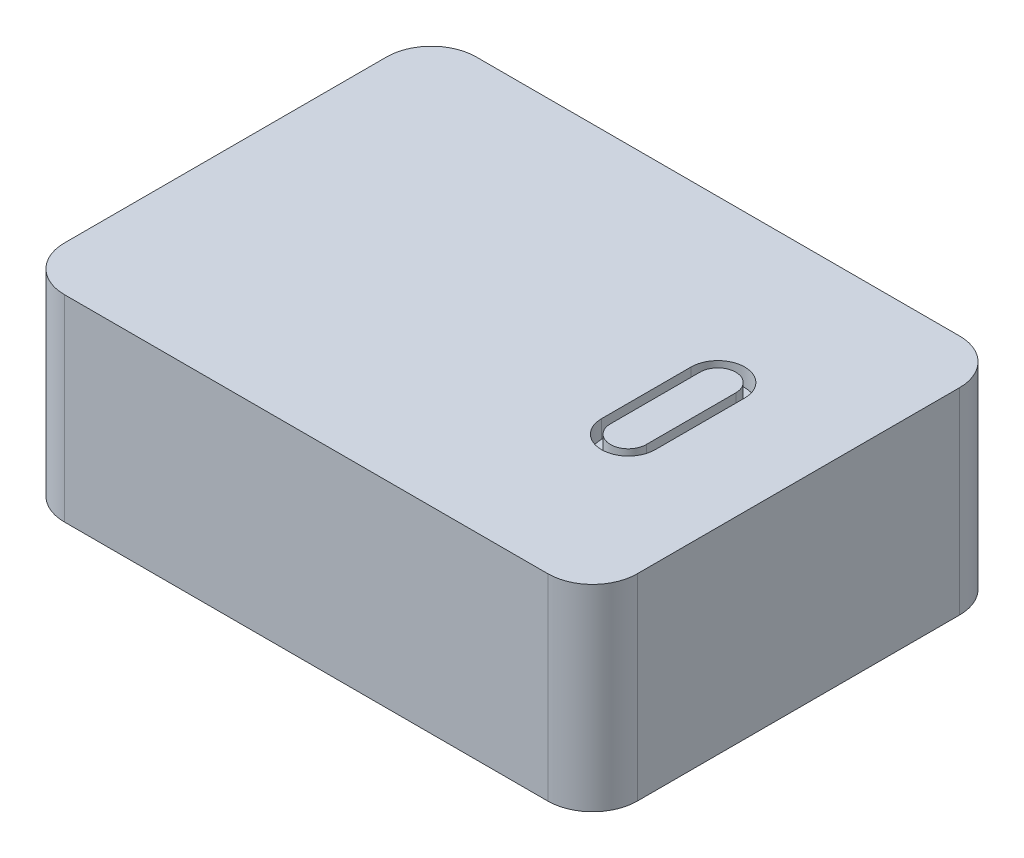
SolidWorks part; units mm, degrees
ref_plane "前视基准面" through (0, 0, 0) normal (0, 0, 1) x (1, 0, 0)
ref_plane "上视基准面" through (0, 0, 0) normal (0, 1, 0) x (1, 0, 0)
ref_plane "右视基准面" through (0, 0, 0) normal (1, 0, 0) x (0, 0, -1)
sketch "草图1" plane through (0, 0, 0) normal (0, 1, 0) x (1, 0, 0)
  line L1 (-32, -23) -> (32, -23)
  line L2 (-32, -23) -> (-32, 23)
  line L3 (-32, 23) -> (32, 23)
  line L4 (32, -23) -> (32, 23)
  line L5 (-32, -23) -> (32, 23) construction
  line L6 (-32, 23) -> (32, -23) construction
  point P0 (0, 0)
  dimension "D1" = 64
  dimension "D2" = 46
extrude "凸台-拉伸1" add sketch "草图1" along normal blind 22
fillet "圆角1" radius 5 4 edges at (-32, 11, -23) (-32, 11, 23) (32, 11, -23) (32, 11, 23)
sketch "草图2" plane through (0, 22, 0) normal (0, 1, 0) x (1, 0, 0)
  line L0 (18, -5) -> (18, 5) construction
  line L1 (15, -5) -> (15, 5)
  line L2 (21, -5) -> (21, 5)
  line L3 (16, -5) -> (16, 5)
  line L6 (20, -5) -> (20, 5)
  arc A0 (15, -5) -> (21, -5) centre (18, -5) ccw
  arc A1 (21, 5) -> (15, 5) centre (18, 5) ccw
  arc A4 (20, 5) -> (16, 5) centre (18, 5) ccw
  arc A5 (16, -5) -> (20, -5) centre (18, -5) ccw
  point P2 (18, 0)
  dimension "D3" = 2
  dimension "D2" = 10
  dimension "D4" = 18
  dimension "D1" = 1
extrude "切除-拉伸1" cut sketch "草图2" against normal blind 2
